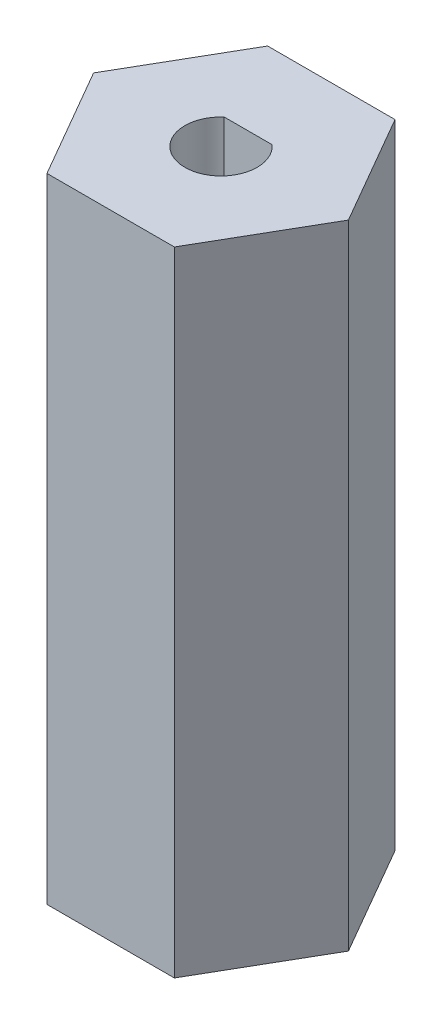
SolidWorks part; units mm, degrees
ref_plane "Front Plane" through (0, 0, 0) normal (0, 0, 1) x (1, 0, 0)
ref_plane "Top Plane" through (0, 0, 0) normal (0, 1, 0) x (1, 0, 0)
ref_plane "Right Plane" through (0, 0, 0) normal (1, 0, 0) x (0, 0, -1)
sketch "Sketch1" plane through (0, 0, 0) normal (0, 1, 0) x (1, 0, 0)
  line L1 (3.5218, 6.1) -> (-3.5218, 6.1)
  line L2 (-3.5218, 6.1) -> (-7.0437, 0)
  line L3 (-7.0437, 0) -> (-3.5218, -6.1)
  line L4 (-3.5218, -6.1) -> (3.5218, -6.1)
  line L5 (3.5218, -6.1) -> (7.0437, 0)
  line L6 (7.0437, 0) -> (3.5218, 6.1)
  circle A0 centre (0, 0) radius 6.1 construction
  dimension "D1" = 12.2
extrude "Boss-Extrude2" add sketch "Sketch1" along normal blind 35
sketch "Sketch6" plane through (0, 0, 0) normal (0, -1, 0) x (1, 0, 0)
  circle A0 centre (0, 0) radius 1.27
  dimension "D1" = 2.54
extrude "Cut-Extrude2" cut sketch "Sketch6" against normal blind 21
sketch "Sketch7" plane through (0, 35, 0) normal (0, 1, 0) x (1, 0, 0)
  line L0 (-1.3229, 1.5) -> (1.3229, 1.5)
  arc A0 (-1.3229, 1.5) -> (1.3229, 1.5) centre (0, 0) ccw
  dimension "D1" = 4
  dimension "D2" = 3.5
extrude "Cut-Extrude3" cut sketch "Sketch7" against normal up to surface (14 mm away) up to face at (0, 21, -1.27)
